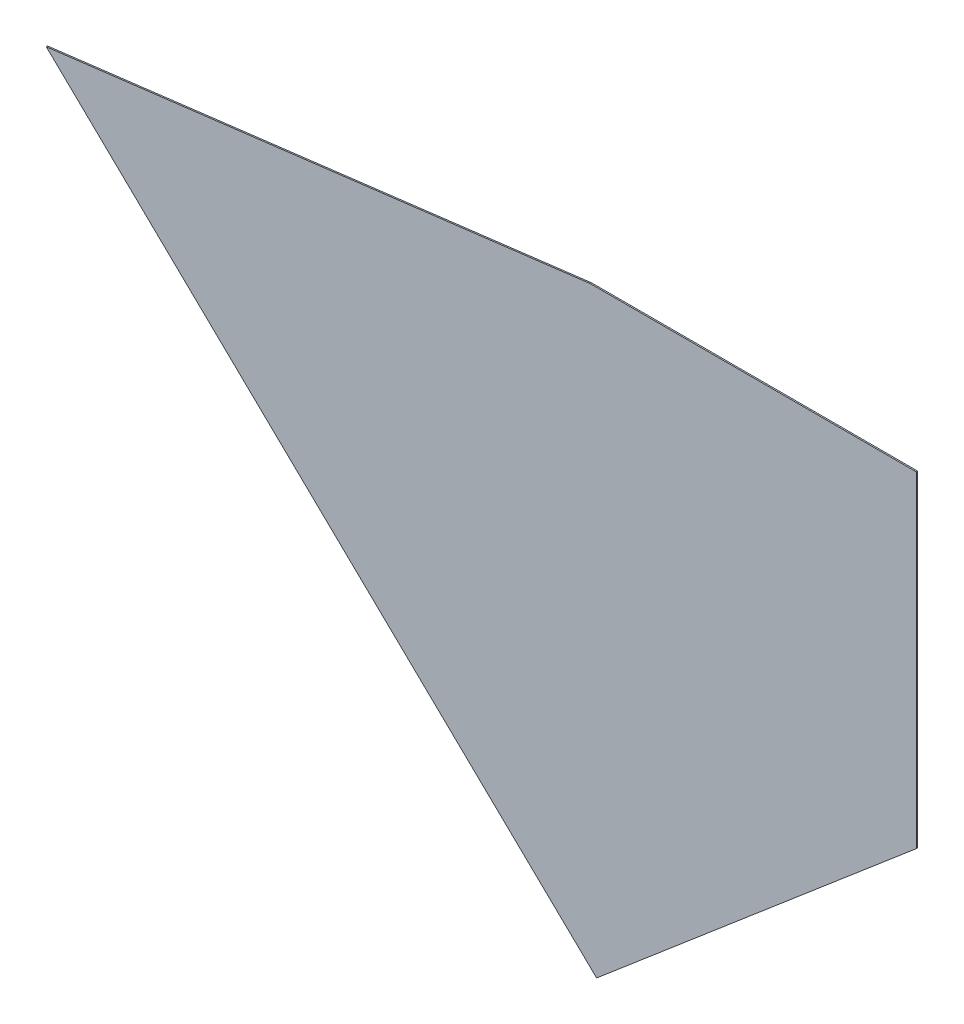
SolidWorks part; units mm, degrees
ref_plane "Front Plane" through (0, 0, 0) normal (0, 0, 1) x (1, 0, 0)
ref_plane "Top Plane" through (0, 0, 0) normal (0, 1, 0) x (1, 0, 0)
ref_plane "Right Plane" through (0, 0, 0) normal (1, 0, 0) x (0, 0, -1)
sketch "Sketch1" plane through (0, 0, 0) normal (0, 0, 1) x (1, 0, 0)
  line L0 (-762, 762) -> (762, -762) construction
  line L1 (-762, 762) -> (762, 762)
  line L4 (762, 762) -> (762, -762)
  line L5 (-3302, 449.58) -> (762, -762) construction
  line L7 (-762, 762) -> (-3302, 449.58)
  line L9 (-3302, 449.58) -> (-731.52, -2032)
  line L10 (-731.52, -2032) -> (762, -762)
  point P0 (0, 0)
  dimension "D1" = 1524
  dimension "D2" = 1524
  dimension "D3" = 3572.8989
  dimension "D4" = 2559.1417
  dimension "D5" = 1960.4851
  dimension "D6" = 4240.7573
extrude "Boss-Extrude1" add sketch "Sketch1" along normal blind 6.35
